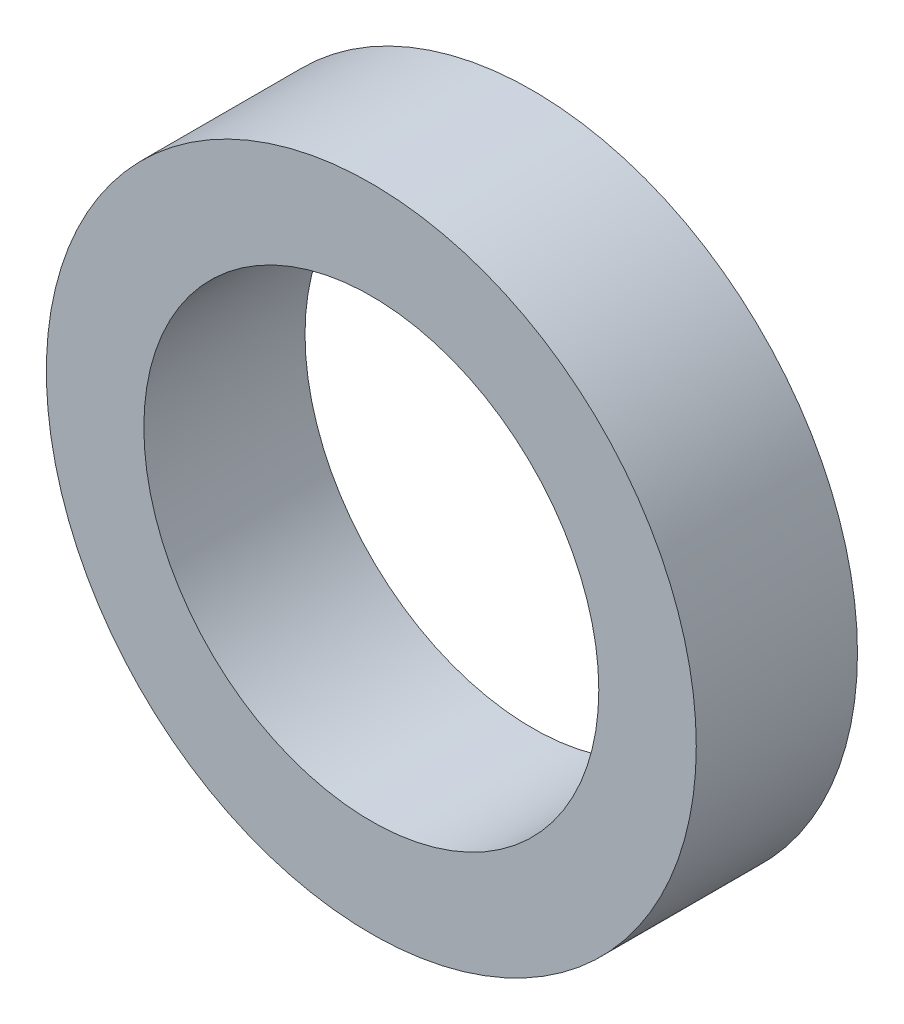
SolidWorks part; units mm, degrees
ref_plane "Front Plane" through (0, 0, 0) normal (0, 0, 1) x (1, 0, 0)
ref_plane "Top Plane" through (0, 0, 0) normal (0, 1, 0) x (1, 0, 0)
ref_plane "Right Plane" through (0, 0, 0) normal (1, 0, 0) x (0, 0, -1)
sketch "Sketch1" plane through (0, 0, 0) normal (0, 0, 1) x (1, 0, 0)
  circle A0 centre (0, 0) radius 15.875
  circle A1 centre (0, 0) radius 11.1125
  dimension "D1" = 22.225
  dimension "D2" = 31.75
extrude "Boss-Extrude1" add sketch "Sketch1" along normal mid plane 7.874
